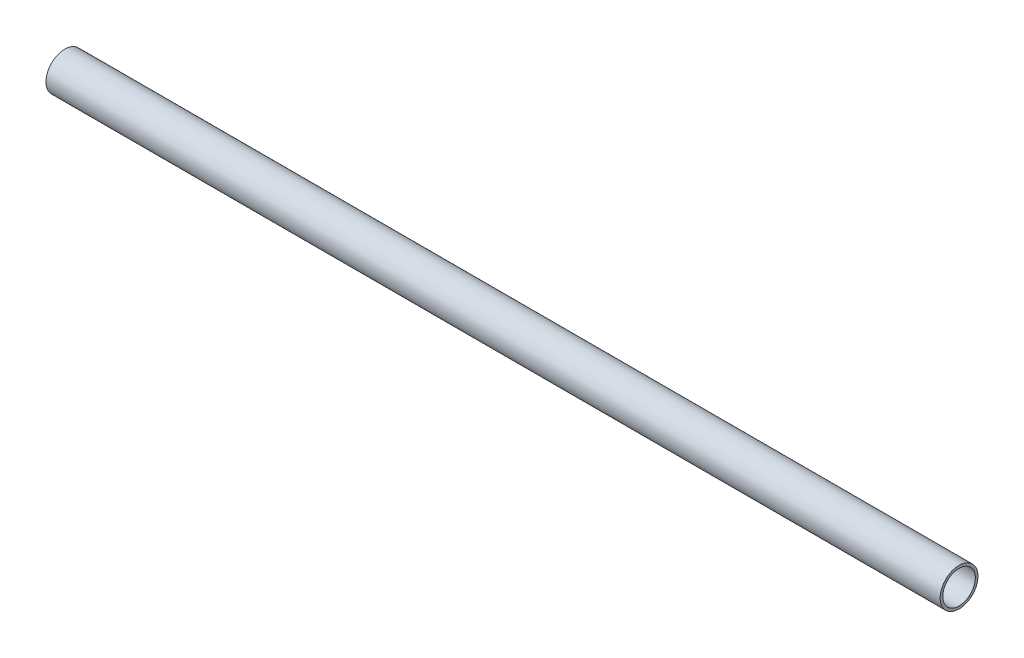
SolidWorks part; units mm, degrees
material "Hexcel AS4C (3000 丝)"
ref_plane "前视基准面" through (0, 0, 0) normal (0, 0, 1) x (1, 0, 0)
ref_plane "上视基准面" through (0, 0, 0) normal (0, 1, 0) x (1, 0, 0)
ref_plane "右视基准面" through (0, 0, 0) normal (1, 0, 0) x (0, 0, -1)
sketch "草图1" plane through (0, 0, 0) normal (0, 0, 1) x (1, 0, 0)
  line L0 (-450, 6.35) -> (-450, 5.461)
  line L1 (-450, 5.461) -> (-150, 5.461)
  line L2 (-150, 5.461) -> (-150, 6.35)
  line L3 (-150, 6.35) -> (-450, 6.35)
  line L4 (-450, 0) -> (0, 0) construction
revolve "旋转1" add sketch "草图1" angle 360 about L4
